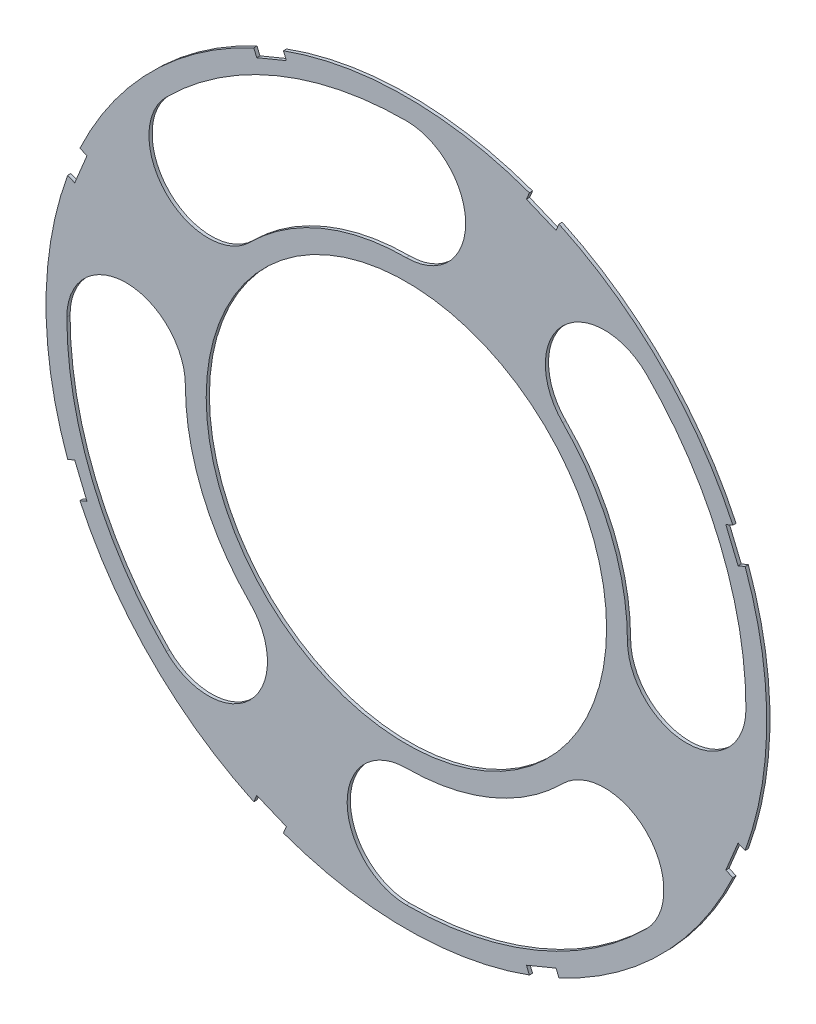
SolidWorks part; units mm, degrees
material "PTFE (general)"
ref_plane "Front Plane" through (0, 0, 0) normal (0, 0, 1) x (1, 0, 0)
ref_plane "Top Plane" through (0, 0, 0) normal (0, 1, 0) x (1, 0, 0)
ref_plane "Right Plane" through (0, 0, 0) normal (1, 0, 0) x (0, 0, -1)
sketch "Sketch4" plane through (0, 0, 0) normal (0, 0, 1) x (1, 0, 0)
  circle A0 centre (0, 0) radius 28.575
  dimension "D1" = 57.15
extrude "Boss-Extrude2" add sketch "Sketch4" along normal blind 0.254
sketch "Sketch5" plane through (0, 0, 0.254) normal (0, 0, 1) x (1, 0, 0)
  circle A0 centre (0, 0) radius 15.875
  circle A1 centre (0, 0) radius 28.575 construction
  dimension "D1" = 12.7
extrude "Cut-Extrude5" cut sketch "Sketch5" against normal through all
sketch "Sketch6" plane through (0, 0, 0.254) normal (0, 0, 1) x (1, 0, 0)
  line L0 (0, 0) -> (36.195, 0) construction
  line L1 (0, 0) -> (20.2056, -20.2056) construction
  line L2 (0, 0) -> (0, -28.575) construction
  line L3 (0, 0) -> (0, -28.575) construction
  line L4 (0, 0) -> (20.2056, -20.2056) construction
  line L5 (0, 0) -> (-20.2056, -20.2056) construction
  line L6 (0, 0) -> (-20.2056, -20.2056) construction
  line L7 (0, 0) -> (-28.575, 0) construction
  line L8 (0, 0) -> (-28.575, 0) construction
  line L9 (0, 0) -> (-20.2056, 20.2056) construction
  line L10 (0, 0) -> (-20.2056, 20.2056) construction
  line L11 (0, 0) -> (0, 28.575) construction
  line L12 (0, 0) -> (0, 28.575) construction
  line L13 (0, 0) -> (12.3928, -12.3928) construction
  line L14 (0, 0) -> (-12.3928, -12.3928) construction
  line L15 (0, 0) -> (20.2056, 20.2056) construction
  line L16 (0, 0) -> (20.2056, 20.2056) construction
  line L17 (0, 0) -> (28.575, 0) construction
  line L18 (0, 0) -> (28.575, 0) construction
  arc A0 (19.0381, 19.0381) -> (12.3928, 12.3928) centre (15.7154, 15.7154) ccw
  circle A1 centre (0, 0) radius 28.575 construction
  arc A2 (19.0381, -19.0381) -> (12.3928, -12.3928) centre (15.7154, -15.7154) ccw
  arc A3 (12.3928, -12.3928) -> (0, -17.526) centre (0, 0) cw
  arc A4 (0, -17.526) -> (0, -26.924) centre (0, -22.225) ccw
  arc A5 (0, -26.924) -> (19.0381, -19.0381) centre (0, 0) ccw
  arc A6 (-19.0381, -19.0381) -> (-12.3928, -12.3928) centre (-15.7154, -15.7154) ccw
  arc A7 (-12.3928, -12.3928) -> (-17.526, 0) centre (0, 0) cw
  arc A8 (-26.924, 0) -> (-19.0381, -19.0381) centre (0, 0) ccw
  arc A9 (-17.526, 0) -> (-26.924, 0) centre (-22.225, 0) ccw
  arc A10 (-19.0381, 19.0381) -> (-12.3928, 12.3928) centre (-15.7154, 15.7154) ccw
  arc A11 (-12.3928, 12.3928) -> (0, 17.526) centre (0, 0) cw
  arc A12 (0, 26.924) -> (-19.0381, 19.0381) centre (0, 0) ccw
  arc A13 (0, 17.526) -> (0, 26.924) centre (0, 22.225) ccw
  arc A14 (12.3928, 12.3928) -> (17.526, 0) centre (0, 0) cw
  arc A15 (26.924, 0) -> (19.0381, 19.0381) centre (0, 0) ccw
  circle A16 centre (0, 0) radius 15.875 construction
  arc A17 (17.526, 0) -> (26.924, 0) centre (22.225, 0) ccw
  point P4 (15.7154, -15.7154)
  point P11 (0, -22.225)
  point P13 (-15.7154, -15.7154)
  point P22 (15.7154, 15.7154)
  point P27 (-22.225, 0)
  point P30 (0, 0)
  point P36 (-15.7154, 15.7154)
  point P41 (0, 22.225)
  point P55 (22.225, 0)
  dimension "D2" = 4
  dimension "D3" = 45
  dimension "D4" = 90
  dimension "D6" = 6.35
  dimension "D7" = 9.398
  dimension "D8" = 4.699
  dimension "D9" = 4.699
  dimension "D5" = 6.35
  dimension "D10" = 90
extrude "Cut-Extrude6" cut sketch "Sketch6" against normal through all
sketch "Sketch8" plane through (0, 0, 0.254) normal (0, 0, 1) x (1, 0, 0)
  line L2 (27.4725, 10.0049) -> (26.5005, 12.3515)
  line L3 (27.4725, 10.0049) -> (26.2992, 9.5188)
  line L4 (26.2992, 9.5188) -> (25.3272, 11.8655)
  line L5 (26.5005, 12.3515) -> (25.3272, 11.8655)
  line L6 (0, 0) -> (50.4438, 0) construction
  line L7 (-10.0049, 27.4725) -> (-12.3515, 26.5005)
  line L8 (-10.0049, 27.4725) -> (-9.5188, 26.2992)
  line L9 (-12.3515, 26.5005) -> (-11.8655, 25.3272)
  line L10 (-9.5188, 26.2992) -> (-11.8655, 25.3272)
  line L11 (-12.3515, 26.5005) -> (-9.5188, 26.2992) construction
  line L12 (-10.0049, 27.4725) -> (-11.8655, 25.3272) construction
  line L13 (-26.5005, 12.3515) -> (-27.4725, 10.0049)
  line L14 (-26.5005, 12.3515) -> (-25.3272, 11.8655)
  line L15 (-25.3272, 11.8655) -> (-26.2992, 9.5188)
  line L16 (-27.4725, 10.0049) -> (-26.2992, 9.5188)
  line L17 (-26.5005, 12.3515) -> (-26.2992, 9.5188) construction
  line L18 (-27.4725, 10.0049) -> (-25.3272, 11.8655) construction
  line L19 (-27.4725, -10.0049) -> (-26.5005, -12.3515)
  line L20 (-27.4725, -10.0049) -> (-26.2992, -9.5188)
  line L21 (-26.2992, -9.5188) -> (-25.3272, -11.8655)
  line L22 (-26.5005, -12.3515) -> (-25.3272, -11.8655)
  line L23 (-27.4725, -10.0049) -> (-25.3272, -11.8655) construction
  line L24 (-26.5005, -12.3515) -> (-26.2992, -9.5188) construction
  line L25 (-12.3515, -26.5005) -> (-10.0049, -27.4725)
  line L26 (-12.3515, -26.5005) -> (-11.8655, -25.3272)
  line L27 (-11.8655, -25.3272) -> (-9.5188, -26.2992)
  line L28 (-10.0049, -27.4725) -> (-9.5188, -26.2992)
  line L29 (-12.3515, -26.5005) -> (-9.5188, -26.2992) construction
  line L30 (-10.0049, -27.4725) -> (-11.8655, -25.3272) construction
  line L31 (10.0049, -27.4725) -> (12.3515, -26.5005)
  line L32 (10.0049, -27.4725) -> (9.5188, -26.2992)
  line L33 (9.5188, -26.2992) -> (11.8655, -25.3272)
  line L34 (12.3515, -26.5005) -> (11.8655, -25.3272)
  line L35 (10.0049, -27.4725) -> (11.8655, -25.3272) construction
  line L36 (12.3515, -26.5005) -> (9.5188, -26.2992) construction
  line L37 (26.5005, -12.3515) -> (27.4725, -10.0049)
  line L38 (26.5005, -12.3515) -> (25.3272, -11.8655)
  line L39 (25.3272, -11.8655) -> (26.2992, -9.5188)
  line L40 (27.4725, -10.0049) -> (26.2992, -9.5188)
  line L41 (26.5005, -12.3515) -> (26.2992, -9.5188) construction
  line L42 (27.4725, -10.0049) -> (25.3272, -11.8655) construction
  line L43 (27.4725, 10.0049) -> (25.3272, 11.8655) construction
  line L44 (26.5005, 12.3515) -> (26.2992, 9.5188) construction
  line L45 (12.3515, 26.5005) -> (10.0049, 27.4725)
  line L46 (12.3515, 26.5005) -> (11.8655, 25.3272)
  line L47 (11.8655, 25.3272) -> (9.5188, 26.2992)
  line L48 (10.0049, 27.4725) -> (9.5188, 26.2992)
  line L49 (12.3515, 26.5005) -> (9.5188, 26.2992) construction
  line L50 (10.0049, 27.4725) -> (11.8655, 25.3272) construction
  circle A0 centre (0, 0) radius 28.575 construction
  point P3 (-10.9352, 26.3999)
  point P11 (-26.3999, 10.9352)
  point P15 (26.3999, 10.9352)
  point P20 (-26.3999, -10.9352)
  point P25 (-10.9352, -26.3999)
  point P26 (0, 0)
  point P31 (10.9352, -26.3999)
  point P36 (26.3999, -10.9352)
  point P45 (10.9352, 26.3999)
  point P46 (0, 0)
  dimension "D5" = 1.27
  dimension "D6" = 2.54
  dimension "D7" = 1.27
  dimension "D9" = 0.635
  dimension "D10" = 112.5
  dimension "D14" = 0.635
  dimension "D21" = 22.5
  dimension "D11" = 8
extrude "Cut-Extrude11" cut sketch "Sketch8" against normal through all
